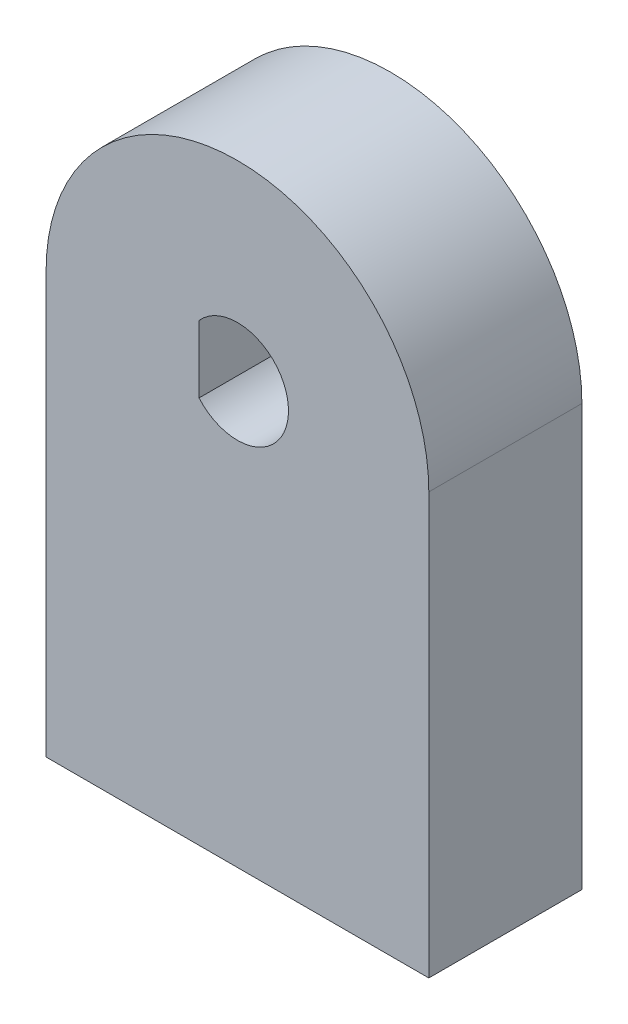
SolidWorks part; units mm, degrees
ref_plane "Front Plane" through (0, 0, 0) normal (0, 0, 1) x (1, 0, 0)
ref_plane "Top Plane" through (0, 0, 0) normal (0, 1, 0) x (1, 0, 0)
ref_plane "Right Plane" through (0, 0, 0) normal (1, 0, 0) x (0, 0, -1)
sketch "Sketch2" plane through (0, 0, 0) normal (0, 0, 1) x (1, 0, 0)
  circle A0 centre (0, 0) radius 15
  circle A1 centre (0, 0) radius 11
  dimension "D1" = 30
  dimension "D2" = 22
extrude "Boss-Extrude1" add sketch "Sketch2" along normal blind 4
sketch "Sketch3" plane through (0, 0, 4) normal (0, 0, 1) x (1, 0, 0)
  circle A0 centre (0, 0) radius 15
  circle A1 centre (0, 0) radius 4
  circle A2 centre (0, 0) radius 15 construction
  dimension "D1" = 8
  dimension "D2" = 0
extrude "Boss-Extrude2" add sketch "Sketch3" along normal blind 8
sketch "Sketch6" plane through (0, 0, 12) normal (0, 0, 1) x (1, 0, 0)
  line L0 (-15, 0) -> (-15, -33)
  line L1 (15, 0) -> (15, -33)
  line L2 (15, -33) -> (-15, -33)
  circle A0 centre (0, 0) radius 15 construction
  circle A2 centre (0, 0) radius 15
  arc A3 (-15, 0) -> (15, 0) centre (0, 0) ccw
  dimension "D1" = 33
  dimension "D2" = 0
extrude "Boss-Extrude5" add sketch "Sketch6" against normal blind 12
sketch "Sketch8" plane through (0, 0, 12) normal (0, 0, 1) x (1, 0, 0)
  line L0 (-3.0138, 2.63) -> (-3.0138, -2.63)
  arc A0 (-3.0138, 2.63) -> (-3.0138, -2.63) centre (0, 0) ccw
  dimension "D2" = 8
  dimension "D1" = 5.26
extrude "Boss-Extrude7" add sketch "Sketch8" against normal blind 8
sketch "Sketch9" plane through (0, -33, 0) normal (0, -1, 0) x (1, 0, 0)
  line L0 (-15, 0) -> (-15, 12) construction
  line L1 (15, 0) -> (15, 12) construction
  line L2 (-15, 0) -> (15, 0) construction
  circle A0 centre (-7, 6) radius 2.875
  circle A1 centre (7, 6) radius 2.875
  point P8 (0, 0)
  point P10 (6.8627, 4.5067)
  dimension "D1" = 5.75
  dimension "D2" = 5.75
  dimension "D3" = 8
  dimension "D4" = 8
  dimension "D5" = 6
  dimension "D6" = 6
extrude "Cut-Extrude1" cut sketch "Sketch9" against normal blind 14
